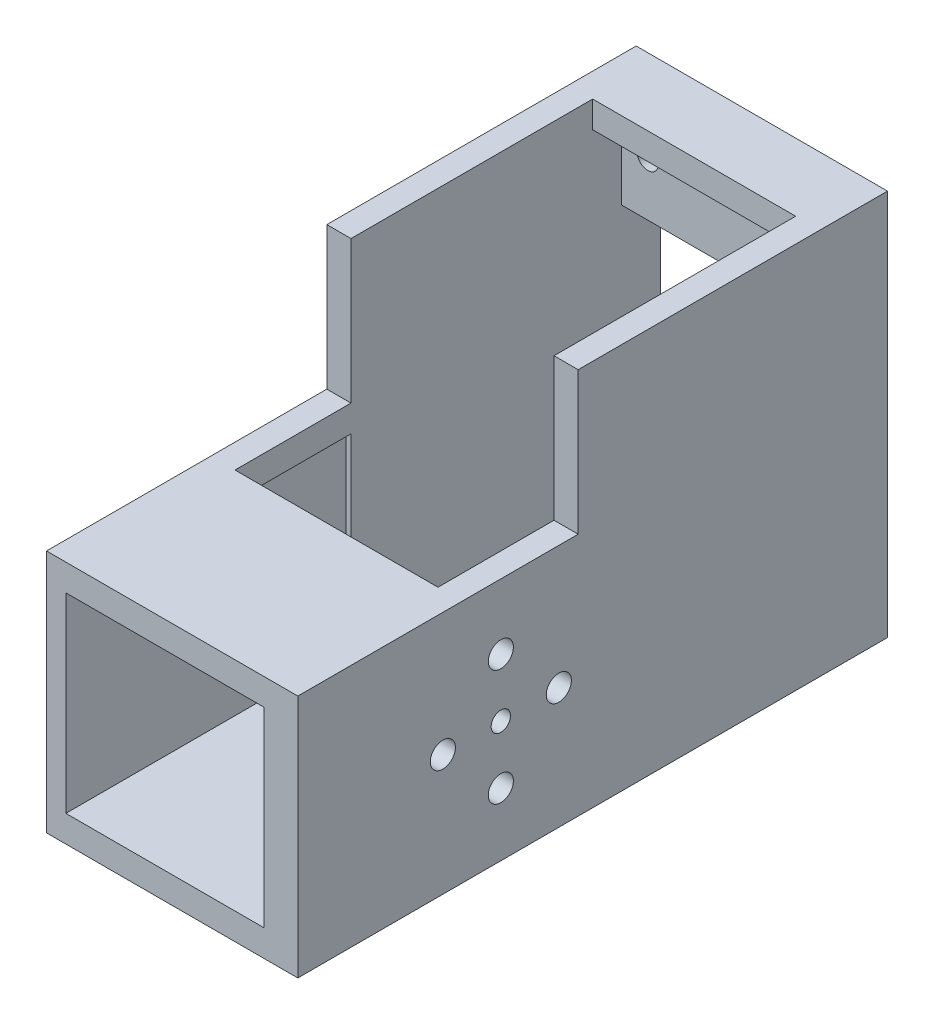
SolidWorks part; units mm, degrees
ref_plane "Front Plane" through (0, 0, 0) normal (0, 0, 1) x (1, 0, 0)
ref_plane "Top Plane" through (0, 0, 0) normal (0, 1, 0) x (1, 0, 0)
ref_plane "Right Plane" through (0, 0, 0) normal (1, 0, 0) x (0, 0, -1)
sketch "Sketch1" plane through (0, 0, 0) normal (0, 0, 1) x (1, 0, 0)
  line L1 (0, 0) -> (-26, 0)
  line L2 (0, 0) -> (0, 40)
  line L3 (0, 40) -> (-26, 40)
  line L4 (-26, 0) -> (-26, 40)
  dimension "D1" = 40
  dimension "D2" = 26
extrude "Boss-Extrude1" add sketch "Sketch1" along normal blind 32
sketch "Sketch2" plane through (0, 0, 32) normal (0, 0, 1) x (1, 0, 0)
  line L0 (-26, 0) -> (0, 0) construction
  line L1 (-23.5, 37.25) -> (-2.5, 37.25)
  line L2 (-23.5, 37.25) -> (-23.5, 2.75)
  line L3 (-23.5, 2.75) -> (-2.5, 2.75)
  line L4 (-2.5, 37.25) -> (-2.5, 2.75)
  line L10 (-26, 40) -> (-26, 0) construction
  dimension "D1" = 34.5
  dimension "D2" = 2.75
  dimension "D3" = 21
  dimension "D4" = 2.5
extrude "Cut-Extrude1" cut sketch "Sketch2" against normal blind 28
sketch "Sketch3" plane through (0, 0, 32) normal (0, 0, 1) x (1, 0, 0)
  line L0 (-26, 40) -> (-26, 0) construction
  line L1 (0, 0) -> (-26, 0)
  line L2 (0, 0) -> (0, 25.26)
  line L3 (0, 25.26) -> (-26, 25.26)
  line L4 (-26, 0) -> (-26, 25.26)
  dimension "D1" = 25.26
extrude "Boss-Extrude2" add sketch "Sketch3" along normal blind 20
sketch "Sketch4" plane through (0, 0, 52) normal (0, 0, 1) x (1, 0, 0)
  line L0 (-26, 0) -> (0, 0) construction
  line L1 (-2, 2.75) -> (-24, 2.75)
  line L2 (-2, 2.75) -> (-2, 22.51)
  line L3 (-2, 22.51) -> (-24, 22.51)
  line L4 (-24, 2.75) -> (-24, 22.51)
  line L7 (0, 0) -> (0, 25.26) construction
  dimension "D1" = 2.75
  dimension "D2" = 19.76
  dimension "D3" = 22
  dimension "D4" = 2
extrude "Cut-Extrude2" cut sketch "Sketch4" against normal blind 20
sketch "Sketch5" plane through (0, 0, 32) normal (0, 0, 1) x (1, 0, 0)
  line L0 (0, 40) -> (-26, 40) construction
  line L1 (-2.5, 37.25) -> (-23.5, 37.25)
  line L2 (-2.5, 37.25) -> (-2.5, 40)
  line L3 (-2.5, 40) -> (-23.5, 40)
  line L4 (-23.5, 37.25) -> (-23.5, 40)
extrude "Cut-Extrude3" cut sketch "Sketch5" against normal blind 25
sketch "Sketch6" plane through (0, 0, 0) normal (0, 0, -1) x (-1, 0, 0)
  line L0 (26, 0) -> (0, 0) construction
  line L3 (0, 0) -> (0, 40) construction
  circle A0 centre (4.8, 4.55) radius 1.1
  circle A1 centre (20.8, 4.55) radius 1.1
  circle A2 centre (20.8, 34.55) radius 1.1
  circle A3 centre (4.8, 34.55) radius 1.1
  dimension "D1" = 4.55
  dimension "D2" = 4.8
  dimension "D3" = 2.2
  dimension "D4" = 2
  dimension "D5" = 2
extrude "Cut-Extrude4" cut sketch "Sketch6" against normal blind 20
sketch "Sketch7" plane through (-26, 0, 0) normal (-1, 0, 0) x (0, 0, 1)
  line L0 (52, 25.26) -> (52, 0) construction
  line L1 (32, 2.75) -> (52, 2.75) construction
  circle A0 centre (40, 12.51) radius 4
  dimension "D1" = 8
  dimension "D2" = 12
  dimension "D3" = 9.76
extrude "Cut-Extrude5" cut sketch "Sketch7" against normal blind 5
sketch "Sketch9" plane through (0, 0, 52) normal (0, 0, 1) x (1, 0, 0)
  line L1 (0, 0) -> (-26, 0)
  line L2 (0, 0) -> (0, 25.26)
  line L3 (0, 25.26) -> (-26, 25.26)
  line L4 (-26, 0) -> (-26, 25.26)
extrude "Cut-Extrude9" cut sketch "Sketch9" against normal blind 3
sketch "Sketch10" plane through (-26, 0, 0) normal (-1, 0, 0) x (0, 0, 1)
  circle A0 centre (40, 12.51) radius 4.8
  circle A1 centre (40, 12.51) radius 4
  dimension "D1" = 9.6
extrude "Boss-Extrude3" add sketch "Sketch10" along normal blind 3
sketch "Sketch13" plane through (0, 0, 4) normal (0, 0, 1) x (1, 0, 0)
  line L0 (-23.5, 20) -> (-23.5, 12)
  line L1 (-23.5, 37.25) -> (-23.5, 2.75) construction
  line L2 (-23.5, 20) -> (-23.5, 29)
  line L3 (-23.5, 12) -> (-2.5, 12)
  line L4 (-2.5, 2.75) -> (-2.5, 37.25) construction
  line L5 (-2.5, 12) -> (-2.5, 29)
  line L6 (-2.5, 29) -> (-23.5, 29)
  dimension "D1" = 8
  dimension "D2" = 9
extrude "Cut-Extrude10" cut sketch "Sketch13" against normal through all
sketch "Sketch14" plane through (0, 0, 49) normal (0, 0, 1) x (1, 0, 0)
  line L0 (-2, 2.75) -> (-3.5, 2.75)
  line L1 (-2, 2.75) -> (-24, 2.75) construction
  line L2 (-3.5, 2.75) -> (-3.5, 22.51)
  line L3 (-24, 22.51) -> (-2, 22.51) construction
  line L4 (-3.5, 22.51) -> (-2, 22.51)
  line L5 (-2, 22.51) -> (-2, 2.75) construction
  line L6 (-2, 22.51) -> (-2, 2.75)
  dimension "D1" = 1.5
extrude "Boss-Extrude5" add sketch "Sketch14" against normal blind 17
sketch "Sketch8" plane through (0, 0, 0) normal (1, 0, 0) x (0, 0, -1)
  line L2 (-32, 2.75) -> (-49, 2.75) construction
  circle A0 centre (-40, 12.51) radius 1
  circle A1 centre (-46, 12.51) radius 1.3
  circle A2 centre (-34, 12.51) radius 1.3
  circle A3 centre (-40, 18.51) radius 1.3
  circle A4 centre (-40, 6.51) radius 1.3
  dimension "D2" = 2
  dimension "D3" = 2.6
  dimension "D4" = 6
  dimension "D5" = 6
  dimension "D6" = 2.6
  dimension "D7" = 6
  dimension "D8" = 2.6
  dimension "D9" = 6
  dimension "D10" = 2.6
  dimension "D11" = 9.76
extrude "Cut-Extrude8" cut sketch "Sketch8" against normal blind 15 and the other way blind 17
sketch "Sketch17" plane through (0, 0, 49) normal (0, 0, 1) x (1, 0, 0)
  line L1 (0, 25.26) -> (-3.5, 25.26)
  line L2 (0, 25.26) -> (0, 2.75)
  line L3 (0, 2.75) -> (-3.5, 2.75)
  line L4 (-3.5, 25.26) -> (-3.5, 2.75)
  line L5 (-26, 25.26) -> (-3.5, 25.26)
  line L6 (-26, 25.26) -> (-26, 22.51)
  line L7 (-26, 22.51) -> (-3.5, 22.51)
  line L8 (-3.5, 25.26) -> (-3.5, 22.51)
  line L9 (-26, 22.51) -> (-24, 22.51)
  line L10 (-26, 22.51) -> (-26, 2.75)
  line L11 (-26, 2.75) -> (-24, 2.75)
  line L12 (-24, 22.51) -> (-24, 2.75)
  line L13 (-26, 0) -> (0, 0)
  line L14 (-26, 0) -> (-26, 2.75)
  line L15 (-26, 2.75) -> (0, 2.75)
  line L16 (0, 0) -> (0, 2.75)
  line M1 (-3.5, 22.51) -> (-3.5, 2.75)
  line M2 (-3.5, 2.75) -> (-24, 2.75)
  line M3 (-24, 2.75) -> (-24, 22.51)
  line M4 (-24, 22.51) -> (-3.5, 22.51)
  line M5 (0, 0) -> (0, 25.26)
  line M6 (0, 25.26) -> (-26, 25.26)
  line M7 (-26, 25.26) -> (-26, 0)
  line M8 (-26, 0) -> (0, 0)
extrude "Boss-Extrude12" add sketch "Sketch17" along normal blind 12 contours L7 L4 M7 M4 M6 | L4 L3 M6 M1 M5 | L11 L3 M7 M8 M5 M2 | L11 L7 M7 M3
sketch "Sketch18" plane through (0, 25.26, 0) normal (0, 1, 0) x (1, 0, 0)
  line L0 (-2.5, -32) -> (-2.5, -44)
  line L1 (-2.5, -44) -> (-23.5, -44)
  line L2 (-23.5, -44) -> (-23.5, -32)
  line L3 (-2.5, -32) -> (-23.5, -32)
  dimension "D1" = 12
extrude "Cut-Extrude11" cut sketch "Sketch18" against normal blind 5
